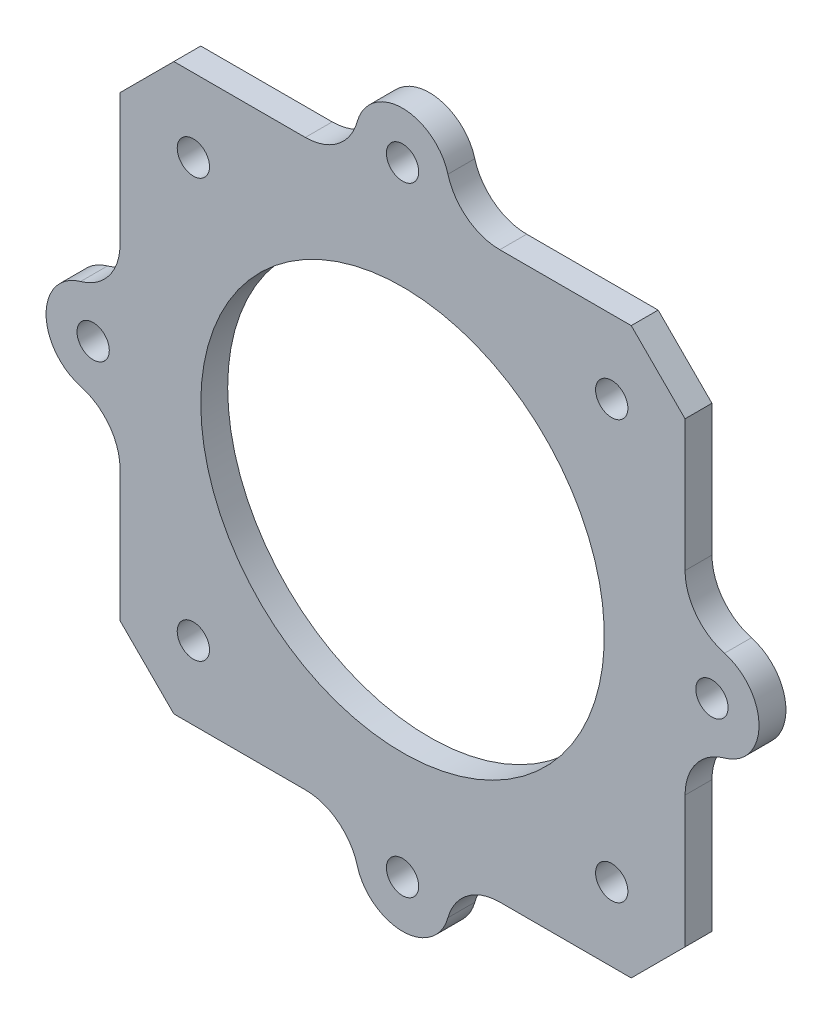
SolidWorks part; units mm, degrees
ref_plane "前视基准面" through (0, 0, 0) normal (0, 0, 1) x (1, 0, 0)
ref_plane "上视基准面" through (0, 0, 0) normal (0, 1, 0) x (1, 0, 0)
ref_plane "右视基准面" through (0, 0, 0) normal (1, 0, 0) x (0, 0, -1)
sketch "草图1" plane through (0, 0, 0) normal (0, 0, 1) x (1, 0, 0)
  line L1 (-21, -21) -> (21, -21)
  line L2 (-21, -21) -> (-21, 21)
  line L3 (-21, 21) -> (21, 21)
  line L4 (21, -21) -> (21, 21)
  line L5 (-21, -21) -> (21, 21) construction
  line L6 (-21, 21) -> (21, -21) construction
  point P0 (0, 0)
  point P6 (0, 0)
  dimension "D1" = 42
  dimension "D2" = 42
extrude "凸台-拉伸1" add sketch "草图1" along normal blind 2
chamfer "倒角1" distance 4 angle 45 4 edges at (-21, 21, 1) (-21, -21, 1) (21, -21, 1) (21, 21, 1)
sketch "草图2" plane through (0, 0, 0) normal (0, 0, -1) x (-1, 0, 0)
  line L0 (0, 15.55) -> (0, -15.55) construction
  line L1 (-15.55, -15.55) -> (15.55, -15.55) construction
  line L2 (-15.55, -15.55) -> (-15.55, 15.55) construction
  line L3 (-15.55, 15.55) -> (15.55, 15.55) construction
  line L4 (15.55, -15.55) -> (15.55, 15.55) construction
  line L5 (-15.55, -15.55) -> (15.55, 15.55) construction
  line L6 (-15.55, 15.55) -> (15.55, -15.55) construction
  line L7 (-15.55, 0) -> (15.55, 0) construction
  circle A0 centre (-15.55, 15.55) radius 1.2
  circle A1 centre (15.55, 15.55) radius 1.2
  circle A2 centre (15.55, -15.55) radius 1.2
  circle A3 centre (-15.55, -15.55) radius 1.2
  point P0 (0, 0)
  dimension "D3" = 2.4
  dimension "D1" = 31.1
  dimension "D2" = 31.1
extrude "切除-拉伸1" cut sketch "草图2" against normal blind 2.5
sketch "草图3" plane through (0, 0, 0) normal (0, 0, -1) x (-1, 0, 0)
  circle A0 centre (0, 0) radius 15
  dimension "D1" = 30
extrude "切除-拉伸2" cut sketch "草图3" against normal blind 2.5
sketch "草图4" plane through (0, 0, 0) normal (0, 0, 1) x (1, 0, 0)
  line L0 (0, 19) -> (0, -21) construction
  line L1 (-19, 3.5) -> (-23, 3.5)
  line L2 (-17, -21) -> (17, -21) construction
  line L3 (-21, 0) -> (19.5, 0) construction
  line L5 (-3.5, 23) -> (-3.5, 19)
  line L6 (-3.5, 19) -> (3.5, 19)
  line L7 (3.5, 23) -> (3.5, 19)
  line L8 (-21, 17) -> (-21, -17) construction
  line L10 (3.5, -23) -> (3.5, -19)
  line L11 (-3.5, -19) -> (3.5, -19)
  line L12 (-3.5, -23) -> (-3.5, -19)
  line L13 (19, -3.5) -> (23, -3.5)
  line L14 (19, -3.5) -> (19, 3.5)
  line L15 (19, 3.5) -> (23, 3.5)
  line L17 (-19, -3.5) -> (-19, 3.5)
  line L18 (-19, -3.5) -> (-23, -3.5)
  arc A1 (3.5, 23) -> (-3.5, 23) centre (0, 23) ccw
  arc A2 (3.5, -23) -> (-3.5, -23) centre (0, -23) cw
  circle A4 centre (0, 23) radius 1.2
  circle A5 centre (0, -23) radius 1.2
  circle A7 centre (23, 0) radius 1.2
  arc A8 (23, -3.5) -> (23, 3.5) centre (23, 0) ccw
  circle A9 centre (-23, 0) radius 1.2
  arc A10 (-23, -3.5) -> (-23, 3.5) centre (-23, 0) cw
  dimension "D3" = 2.4
  dimension "D6" = 2.4
  dimension "D1" = 7
  dimension "D2" = 4
  dimension "D4" = 7
  dimension "D5" = 4
extrude "凸台-拉伸2" add sketch "草图4" along normal blind 2 contours L7 A1 L5 L6 A4 | A2 L10 L11 L12 A5 | A10 L18 L17 L1 A9 | L13 A8 L15 L14 A7
fillet "圆角1" radius 4 8 edges at (-21, 3.5, 1) (-21, -3.5, 1) (-3.5, -21, 1) (3.5, -21, 1) (21, -3.5, 1) (21, 3.5, 1) (3.5, 21, 1) (-3.5, 21, 1)
